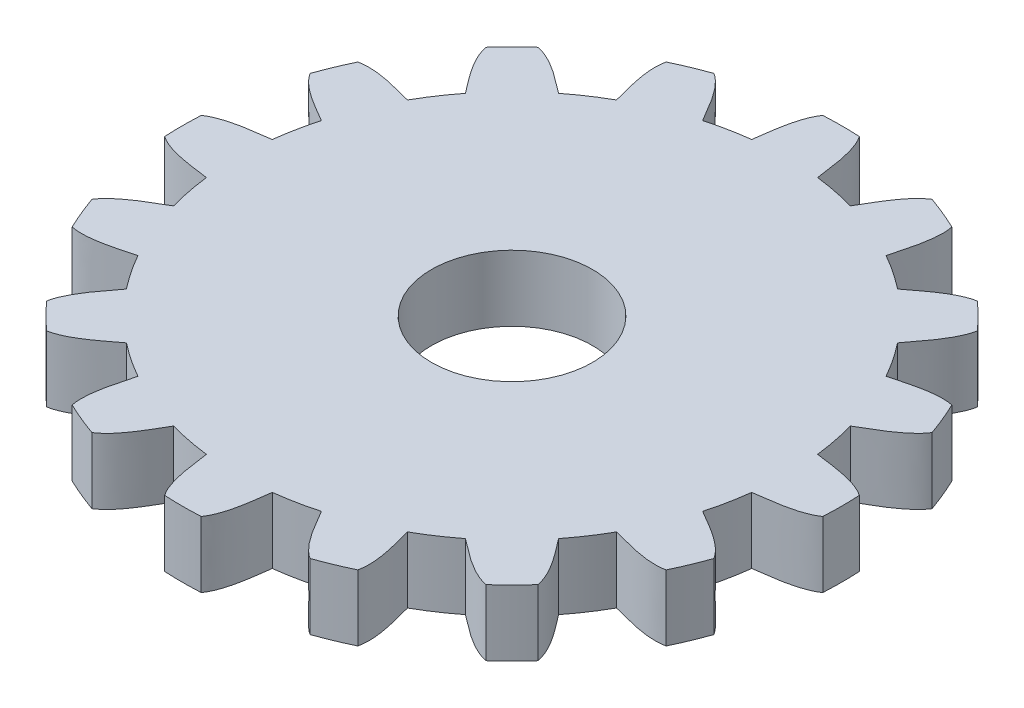
SolidWorks part; units mm, degrees
ref_plane "Front Plane" through (0, 0, 0) normal (0, 0, 1) x (1, 0, 0)
ref_plane "Top Plane" through (0, 0, 0) normal (0, 1, 0) x (1, 0, 0)
ref_plane "Right Plane" through (0, 0, 0) normal (1, 0, 0) x (0, 0, -1)
sketch "Sketch1" plane through (0, 0, 0) normal (0, 1, 0) x (1, 0, 0)
  circle A0 centre (0, 0) radius 2.2 construction
  circle A1 centre (0, 0) radius 1.5
  dimension "D1" = 4.4
  dimension "D2" = 3
extrude "Boss-Extrude1" add sketch "Sketch1" along normal blind 0.36
sketch "Sketch2" plane through (0, 0, 0) normal (0, 1, 0) x (1, 0, 0)
  line L0 (0, 0) -> (0, -2.5308) construction
  circle A0 centre (0, 0) radius 1.8 construction
  circle A2 centre (0, 0) radius 1.5 construction
  arc A3 (-0.18, -1.4892) -> (0.18, -1.4892) centre (0, 0) ccw
  arc A4 (-0.1, -1.7972) -> (0.1, -1.7972) centre (0, 0) ccw
  spline S0 degree 3 poles (-0.18, -1.4892) (-0.1655, -1.5915) (-0.1537, -1.7193) (-0.1, -1.7972) knots 0 0 0 0 1 1 1 1
  spline S1 degree 3 poles (0.18, -1.4892) (0.1655, -1.5915) (0.1537, -1.7193) (0.1, -1.7972) knots 0 0 0 0 1 1 1 1
  dimension "D1" = 3.6
  dimension "D2" = 0.1
  dimension "D3" = 0.18
extrude "Boss-Extrude2" add sketch "Sketch2" along normal up to surface (0.36 mm away) up to face at (0, 0.36, 1.5)
pattern_circular "CirPattern1" count 16 over 360 about axis through (0, 0.36, 0) along (0, -1, 0) of "Boss-Extrude2"
sketch "Sketch3" plane through (0, 0.36, 0) normal (0, 1, 0) x (1, 0, 0)
  circle A0 centre (0, 0) radius 0.44
  dimension "D1" = 0.88
extrude "Cut-Extrude1" cut sketch "Sketch3" against normal through all
